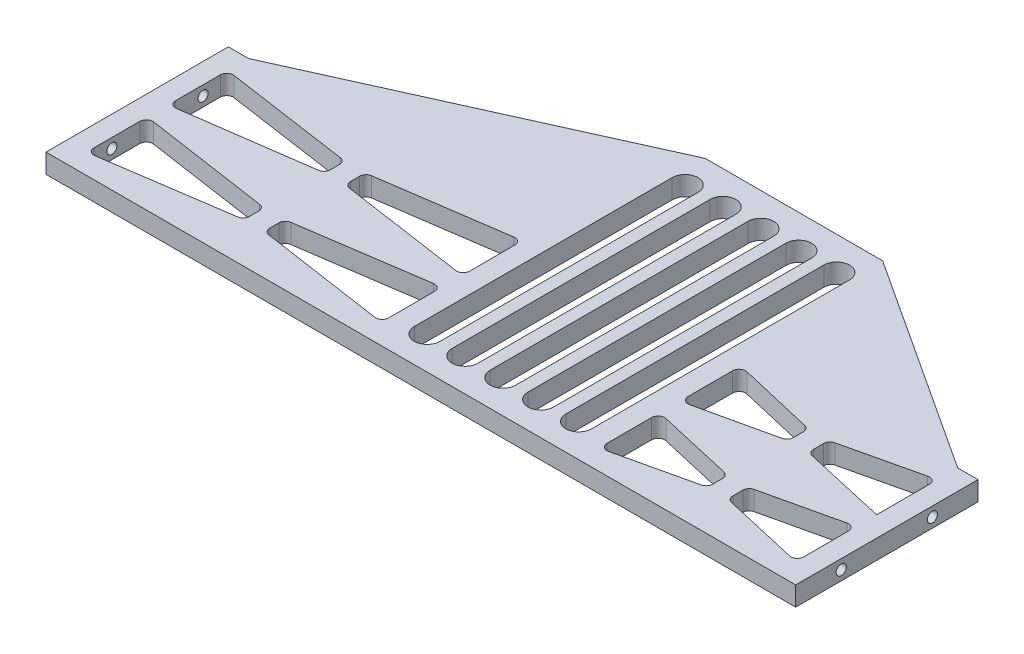
SolidWorks part; units mm, degrees
material "6061-T6 (SS)"
ref_plane "Front Plane" through (0, 0, 0) normal (0, 0, 1) x (1, 0, 0)
ref_plane "Top Plane" through (0, 0, 0) normal (0, 1, 0) x (1, 0, 0)
ref_plane "Right Plane" through (0, 0, 0) normal (1, 0, 0) x (0, 0, -1)
sketch "Sketch2" plane through (0, 0, 0) normal (0, 1, 0) x (1, 0, 0)
  line L0 (0, 0) -> (-143, 0) construction
  line L1 (0, 0) -> (120.3766, 0) construction
  line L2 (-66.5, -22.5) -> (118.5, -22.5)
  line L3 (-66.5, 2.5) -> (118.5, 2.5) construction
  line L4 (118.5, -22.5) -> (118.5, 22.5)
  line L5 (-66.5, 22.5) -> (-66.5, -22.5)
  line L6 (-66.5, 22.5) -> (-61.5, 22.5)
  line L7 (11.213, 69.9107) -> (11.213, -35.2309) construction
  line L8 (-66.5, 22.5) -> (150.026, 22.5) construction
  line L9 (150.026, 22.5) -> (150.026, -22.5) construction
  line L10 (150.026, -22.5) -> (118.5, -22.5) construction
  line L11 (113.5, 22.5) -> (118.5, 22.5)
  line L12 (41.263, -40.0137) -> (150.026, -40.0137) construction
  line L13 (47.438, 49.325) -> (47.438, -14.325) construction
  line L14 (50.613, 49.325) -> (50.613, -14.325)
  line L15 (19.388, 49.325) -> (19.388, -14.325) construction
  line L16 (44.263, 49.325) -> (44.263, -14.325)
  line L17 (38.088, 49.325) -> (38.088, -14.325) construction
  line L18 (64.963, -35.076) -> (64.963, 69.9107) construction
  line L19 (41.263, 49.325) -> (41.263, -14.325)
  line L20 (34.913, 49.325) -> (34.913, -14.325)
  line L21 (28.738, 49.325) -> (28.738, -14.325) construction
  line L22 (31.913, 49.325) -> (31.913, -14.325)
  line L23 (25.563, 49.325) -> (25.563, -14.325)
  line L24 (56.788, 49.325) -> (56.788, -14.325) construction
  line L25 (59.963, 49.325) -> (59.963, -14.325)
  line L26 (53.613, 49.325) -> (53.613, -14.325)
  line L27 (22.563, 49.325) -> (22.563, -14.325)
  line L28 (118.5, 2.5) -> (118.5, -2.5) construction
  line L29 (118.5, -2.5) -> (-66.5, -2.5) construction
  line L30 (-61.5, 22.5) -> (-61.5, -22.5) construction
  line L31 (-61.5, -17.5) -> (118.5, -17.5) construction
  line L32 (113.5, 22.5) -> (113.5, -22.5) construction
  line L33 (86.7315, -17.5) -> (86.7315, 22.5) construction
  line L34 (91.7315, -17.5) -> (91.7315, 22.5) construction
  line L35 (11.213, 17.3399) -> (-61.5, 17.3399) construction
  line L36 (-27.6435, 22.5) -> (-27.6435, -17.5) construction
  line L37 (-22.6435, 22.5) -> (-22.6435, -17.5) construction
  line L38 (-58.937, 57.5) -> (116.063, 57.5) construction
  line L39 (16.213, 49.325) -> (16.213, -14.325)
  line L40 (-61.5, 22.5) -> (16.213, 57.5)
  line L41 (16.213, 57.5) -> (59.963, 57.5)
  line L42 (59.963, 57.5) -> (113.5, 22.5)
  line L43 (-25.1435, 17.3399) -> (-25.1435, 2.5) construction
  line L44 (-25.1435, -17.5) -> (-25.1435, -2.5) construction
  line L45 (-59.6842, 17.0761) -> (-29.0027, 12.6175)
  line L46 (-27.6435, 11.0465) -> (-27.6435, 8.8006)
  line L47 (-29.0107, 7.2284) -> (-59.6922, 2.9299)
  line L48 (-61.5, 4.5021) -> (-61.5, 15.5051)
  line L49 (-59.6806, -2.7687) -> (-28.9991, -7.2998)
  line L50 (-27.6435, -8.8703) -> (-27.6435, -11.1297)
  line L51 (-28.9991, -12.7002) -> (-59.6806, -17.2313)
  line L52 (-61.5, -15.6608) -> (-61.5, -4.3392)
  line L53 (-22.6435, -8.8703) -> (-22.6435, -11.1297)
  line L54 (64.963, 17.5) -> (113.5, 17.5) construction
  line L55 (-21.2879, -12.7002) -> (9.3936, -17.2313)
  line L56 (11.213, -15.6608) -> (11.213, -4.3392)
  line L57 (9.3936, -2.7687) -> (-21.2879, -7.2998)
  line L58 (-22.6435, 8.7934) -> (-22.6435, 11.0465)
  line L59 (-21.2843, 12.6175) -> (9.3972, 17.0761)
  line L60 (11.213, 15.5051) -> (11.213, 4.3349)
  line L61 (9.3972, 2.7639) -> (-21.2843, 7.2224)
  line L62 (64.963, 15.4994) -> (64.963, 4.4863)
  line L63 (66.9005, 2.9379) -> (85.494, 7.1403)
  line L64 (86.7315, 8.6887) -> (86.7315, 11.1603)
  line L65 (85.5048, 12.7062) -> (66.9113, 17.0453)
  line L66 (91.7315, 11.1603) -> (91.7315, 8.6887)
  line L67 (92.969, 7.1403) -> (113.5, 2.5)
  line L68 (113.5, 2.5) -> (113.5, 15.4994)
  line L69 (111.5517, 17.0453) -> (92.9582, 12.7062)
  line L70 (86.7315, -8.7642) -> (86.7315, -11.2358)
  line L71 (85.4994, -12.783) -> (66.9059, -17.0537)
  line L72 (64.963, -15.5065) -> (64.963, -4.4935)
  line L73 (16.213, 52.5) -> (59.963, 52.5) construction
  line L74 (66.9059, -2.9463) -> (85.4994, -7.217)
  line L75 (91.7315, -8.7642) -> (91.7315, -11.2358)
  line L76 (92.9636, -12.783) -> (111.5571, -17.0537)
  line L77 (113.5, -15.5065) -> (113.5, -4.4935)
  line L78 (92.9636, -7.217) -> (111.5571, -2.9463)
  arc A0 (50.613, 49.325) -> (44.263, 49.325) centre (47.438, 49.325) ccw
  arc A1 (44.263, -14.325) -> (50.613, -14.325) centre (47.438, -14.325) ccw
  arc A2 (41.263, 49.325) -> (34.913, 49.325) centre (38.088, 49.325) ccw
  arc A3 (34.913, -14.325) -> (41.263, -14.325) centre (38.088, -14.325) ccw
  arc A4 (31.913, 49.325) -> (25.563, 49.325) centre (28.738, 49.325) ccw
  arc A5 (25.563, -14.325) -> (31.913, -14.325) centre (28.738, -14.325) ccw
  arc A6 (59.963, 49.325) -> (53.613, 49.325) centre (56.788, 49.325) ccw
  arc A7 (53.613, -14.325) -> (59.963, -14.325) centre (56.788, -14.325) ccw
  arc A8 (22.563, 49.325) -> (16.213, 49.325) centre (19.388, 49.325) ccw
  arc A9 (16.213, -14.325) -> (22.563, -14.325) centre (19.388, -14.325) ccw
  arc A10 (113.5, 15.4994) -> (111.5517, 17.0453) centre (111.9125, 15.4994) ccw
  arc A11 (91.7315, 11.1603) -> (92.9582, 12.7062) centre (93.319, 11.1603) cw
  arc A12 (91.7315, 8.6887) -> (92.969, 7.1403) centre (93.319, 8.6887) ccw
  arc A13 (113.5, -4.4935) -> (111.5571, -2.9463) centre (111.9125, -4.4935) ccw
  arc A14 (111.5571, -17.0537) -> (113.5, -15.5065) centre (111.9125, -15.5065) ccw
  arc A15 (91.7315, -11.2358) -> (92.9636, -12.783) centre (93.319, -11.2358) ccw
  arc A16 (91.7315, -8.7642) -> (92.9636, -7.217) centre (93.319, -8.7642) cw
  arc A17 (86.7315, -11.2358) -> (85.4994, -12.783) centre (85.144, -11.2358) cw
  arc A18 (86.7315, -8.7642) -> (85.4994, -7.217) centre (85.144, -8.7642) ccw
  arc A19 (64.963, -15.5065) -> (66.9059, -17.0537) centre (66.5505, -15.5065) ccw
  arc A20 (64.963, -4.4935) -> (66.9059, -2.9463) centre (66.5505, -4.4935) cw
  arc A21 (86.7315, 8.6887) -> (85.494, 7.1403) centre (85.144, 8.6887) cw
  arc A22 (86.7315, 11.1603) -> (85.5048, 12.7062) centre (85.144, 11.1603) ccw
  arc A23 (64.963, 4.4863) -> (66.9005, 2.9379) centre (66.5505, 4.4863) ccw
  arc A24 (64.963, 15.4994) -> (66.9113, 17.0453) centre (66.5505, 15.4994) cw
  arc A25 (11.213, 4.3349) -> (9.3972, 2.7639) centre (9.6255, 4.3349) cw
  arc A26 (11.213, 15.5051) -> (9.3972, 17.0761) centre (9.6255, 15.5051) ccw
  arc A27 (-22.6435, 8.7934) -> (-21.2843, 7.2224) centre (-21.056, 8.7934) ccw
  arc A28 (-22.6435, 11.0465) -> (-21.2843, 12.6175) centre (-21.056, 11.0465) cw
  arc A29 (9.3936, -17.2313) -> (11.213, -15.6608) centre (9.6255, -15.6608) ccw
  arc A30 (11.213, -4.3392) -> (9.3936, -2.7687) centre (9.6255, -4.3392) ccw
  arc A31 (-22.6435, -8.8703) -> (-21.2879, -7.2998) centre (-21.056, -8.8703) cw
  arc A32 (-22.6435, -11.1297) -> (-21.2879, -12.7002) centre (-21.056, -11.1297) ccw
  arc A33 (-28.9991, -12.7002) -> (-27.6435, -11.1297) centre (-29.231, -11.1297) ccw
  arc A34 (-27.6435, -8.8703) -> (-28.9991, -7.2998) centre (-29.231, -8.8703) ccw
  arc A35 (-61.5, -15.6608) -> (-59.6806, -17.2313) centre (-59.9125, -15.6608) ccw
  arc A36 (-61.5, -4.3392) -> (-59.6806, -2.7687) centre (-59.9125, -4.3392) cw
  arc A37 (-27.6435, 8.8006) -> (-29.0107, 7.2284) centre (-29.231, 8.8006) cw
  arc A38 (-27.6435, 11.0465) -> (-29.0027, 12.6175) centre (-29.231, 11.0465) ccw
  arc A39 (-61.5, 4.5021) -> (-59.6922, 2.9299) centre (-59.9125, 4.5021) ccw
  arc A40 (-59.6842, 17.0761) -> (-61.5, 15.5051) centre (-59.9125, 15.5051) ccw
  point P6 (-61.5, 22.5)
  point P9 (128.026, 22.5)
  point P10 (19.388, -17.5)
  point P11 (16.213, 57.5)
  point P12 (26, -22.5)
  point P15 (38.088, 49.325)
  point P16 (38.088, -14.325)
  point P17 (-66.5, 22.5)
  point P18 (47.438, 17.5)
  point P19 (47.438, 49.325)
  point P20 (-66.5, -22.5)
  point P21 (113.5, 22.5)
  point P22 (113.5, -22.5)
  point P24 (59.963, 57.5)
  point P25 (-25.1435, 17.3399)
  point P29 (56.788, -14.325)
  point P33 (28.738, 49.325)
  point P35 (28.738, -14.325)
  point P36 (47.438, -14.325)
  point P38 (38.088, 17.5)
  point P46 (28.738, 17.5)
  point P57 (-66.5, 0)
  point P58 (56.788, 49.325)
  point P61 (56.788, 17.5)
  point P70 (9.7565, -35.076)
  point P76 (64.963, -17.5)
  point P78 (36.7, -22.5)
  point P79 (89.2315, 17.5)
  point P80 (86.7315, -17.5)
  point P81 (91.7315, -17.5)
  point P87 (-27.6435, -17.5)
  point P88 (-22.6435, -17.5)
  point P96 (19.388, 17.5)
  point P100 (11.213, 2.5)
  point P101 (11.213, -17.5)
  point P102 (11.213, -2.5)
  point P106 (41.263, -22.5)
  point P111 (-25.1435, -10)
  point P112 (-25.1435, 9.92)
  point P113 (-27.6435, 12.42)
  point P114 (-27.6435, 7.42)
  point P115 (-27.6435, -7.5)
  point P116 (-27.6435, -12.5)
  point P117 (-22.6435, 12.42)
  point P118 (11.213, 2.5)
  point P119 (-22.6435, 7.42)
  point P120 (-22.6435, -7.5)
  point P121 (-22.6435, -12.5)
  point P122 (86.7315, 12.42)
  point P123 (86.7315, 7.42)
  point P124 (91.7315, 12.42)
  point P125 (91.7315, 7.42)
  point P126 (86.7315, -7.5)
  point P127 (86.7315, -12.5)
  point P128 (91.7315, -12.5)
  point P129 (91.7315, -7.5)
  point P130 (-61.5, -2.5)
  point P131 (11.213, -17.5)
  point P134 (11.213, -2.5)
  point P136 (113.5, -17.5)
  point P139 (11.213, -17.5)
  point P144 (11.213, -2.5)
  point P151 (11.213, 2.5)
  point P155 (-61.5, 2.6766)
  point P163 (-61.5, 2.6766)
  point P170 (56.788, -17.5)
  point P171 (47.438, -17.5)
  point P172 (38.088, -17.5)
  point P173 (28.738, -17.5)
  point P175 (91.7315, 12.42)
  point P176 (64.963, 17.5)
  point P179 (64.963, 22.5)
  point P181 (113.5, 2.5)
  point P183 (91.7315, 7.42)
  point P186 (113.5, -2.5)
  point P188 (64.963, 2.5)
  point P189 (-61.5, 2.6766)
  point P191 (113.5, -17.5)
  point P194 (113.5, -2.5)
  point P195 (91.7315, -12.5)
  point P198 (91.7315, -7.5)
  point P201 (86.7315, -12.5)
  point P203 (64.963, -2.5)
  point P205 (86.7315, -7.5)
  point P208 (64.963, -17.5)
  point P211 (64.963, -2.5)
  point P214 (64.963, -2.5)
  point P215 (86.7315, 7.42)
  point P216 (64.963, -2.5)
  point P217 (64.963, -17.5)
  point P220 (86.7315, 12.42)
  point P221 (64.963, -17.5)
  point P224 (64.963, 2.5)
  point P230 (11.213, 2.5)
  point P232 (135.026, -17.5)
  point P237 (-22.6435, 7.42)
  point P240 (113.5, 2.5)
  point P241 (135.026, -17.5)
  point P242 (-22.6435, 12.42)
  point P245 (113.5, -2.5)
  point P246 (11.213, -17.5)
  point P249 (113.5, 2.5)
  point P250 (11.213, -2.5)
  point P253 (-22.6435, -7.5)
  point P256 (-22.6435, -12.5)
  point P259 (-27.6435, -12.5)
  point P261 (28.738, 52.5)
  point P263 (-27.6435, -7.5)
  point P265 (11.213, 55)
  point P266 (64.963, 55)
  point P274 (-61.5, -2.5)
  point P277 (-27.6435, 7.42)
  point P279 (64.963, 2.5)
  point P281 (-27.6435, 12.42)
  point P284 (-61.5, 2.6766)
  point P304 (64.963, 22.5)
  point P305 (64.963, 22.5)
  dimension "D2" = 22
  dimension "D4" = 2.5
  dimension "D3" = 5
  dimension "D5" = 3
  dimension "D9" = 3
  dimension "D11" = 5
  dimension "D13" = 5
  dimension "D16" = 5
  dimension "D6" = 216.526
  dimension "D7" = 5
  dimension "D22" = 5
  dimension "D17" = 2.5
  dimension "D24" = 1.5875
  dimension "D1" = 9.526
  dimension "D8" = 3
  dimension "D10" = 3
  dimension "D12" = 2.5
  dimension "D14" = 5
  dimension "D15" = 5
  dimension "D18" = 2.5
  dimension "D19" = 5
  dimension "D20" = 5
  dimension "D21" = 2.5
  dimension "D23" = 80
  dimension "D26" = 5
  dimension "D28" = 5
  dimension "D29" = 185
extrude "Boss-Extrude1" add sketch "Sketch2" along normal blind 4.763
hole_wizard "Tap Drill for M3x0.5 Tap1" positions "Sketch4" profile "Sketch3" hole size "M3x0.5" standard "ANSI Metric" end condition up to next
sketch "Sketch4" plane through (118.5, 0, 0) normal (1, 0, 0) x (0, 0, -1)
  line L0 (-22.5, 2.3815) -> (22.5, 2.3815) construction
  line L1 (-22.5, 4.763) -> (-22.5, 0) construction
  line L2 (22.5, 4.763) -> (22.5, 0) construction
  point P0 (-11.25, 2.3815)
  point P2 (11.25, 2.3815)
  dimension "D1" = 11.25
  dimension "D2" = 11.25
sketch "Sketch3" plane through (118.5, 2.3815, 11.25) normal (0, 1, 0) x (0, 0, -1)
  line L0 (0, 0) -> (0, 5)
  line L1 (0, 5) -> (1.25, 5)
  line L2 (1.25, 5) -> (1.25, 0)
  line L5 (1.25, 0) -> (0, 0)
  line L11 (0, -6.35) -> (0, 107.95) construction
  dimension "Thru Hole Dia." = 2.5
  dimension "Thru Hole Depth" = 5
hole_wizard "Tap Drill for M3x0.5 Tap2" positions "Sketch6" profile "Sketch5" hole size "M3x0.5" standard "ANSI Metric" end condition up to next
sketch "Sketch6" plane through (-66.5, 0, 0) normal (-1, 0, 0) x (0, 0, 1)
  line L0 (-22.5, 2.3815) -> (22.5, 2.3815) construction
  line L1 (-22.5, 4.763) -> (-22.5, 0) construction
  line L2 (22.5, 4.763) -> (22.5, 0) construction
  point P0 (11.25, 2.3815)
  point P2 (-11.25, 2.3815)
  dimension "D1" = 11.25
  dimension "D2" = 11.25
sketch "Sketch5" plane through (-66.5, 2.3815, 11.25) normal (0, 1, 0) x (0, 0, 1)
  line L0 (0, 0) -> (0, 5)
  line L1 (0, 5) -> (1.25, 5)
  line L2 (1.25, 5) -> (1.25, 0)
  line L5 (1.25, 0) -> (0, 0)
  line L11 (0, -6.35) -> (0, 107.95) construction
  dimension "Thru Hole Dia." = 2.5
  dimension "Thru Hole Depth" = 5
